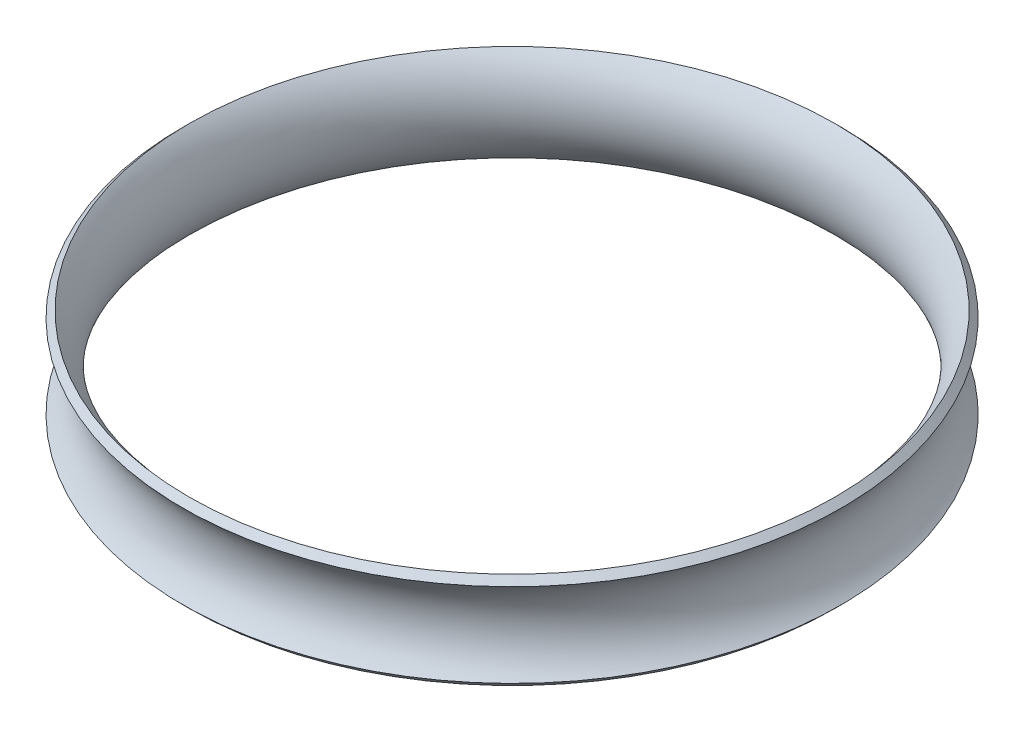
SolidWorks part; units mm, degrees
ref_plane "Front Plane" through (0, 0, 0) normal (0, 0, 1) x (1, 0, 0)
ref_plane "Top Plane" through (0, 0, 0) normal (0, 1, 0) x (1, 0, 0)
ref_plane "Right Plane" through (0, 0, 0) normal (1, 0, 0) x (0, 0, -1)
sketch "Sketch1" plane through (0, 0, 0) normal (0, 1, 0) x (1, 0, 0)
  circle A0 centre (0, 0) radius 92.9864
sketch "Sketch2" plane through (0, 0, 0) normal (0, 0, 1) x (1, 0, 0)
  line L0 (0, 0) -> (0, 23.7148)
  point P3 (0, 0)
  point P4 (0, 0)
  point P5 (0, 0)
  point P6 (0, 0)
  point P7 (0, 0)
  point P8 (0, 0)
  dimension "D1" = 23.7148
ref_plane "Plane1" through (0, 23.622, 0) normal (0, 1, 0) x (1, 0, 0)
sketch "Sketch4" plane through (0, 23.622, 0) normal (0, 1, 0) x (1, 0, 0)
  circle A0 centre (0, 0) radius 92.9864
sketch "Sketch5" plane through (0, 0, 0) normal (0, 0, 1) x (1, 0, 0)
  line L0 (92.9864, 23.622) -> (-92.9864, 23.622) construction
  line L1 (92.9864, 0) -> (-92.9864, 0) construction
  arc A0 (92.9864, 23.622) -> (92.9864, 0) centre (104.7974, 11.811) ccw
revolve "Revolve-Thin1" add sketch "Sketch5" angle 360 about L0
